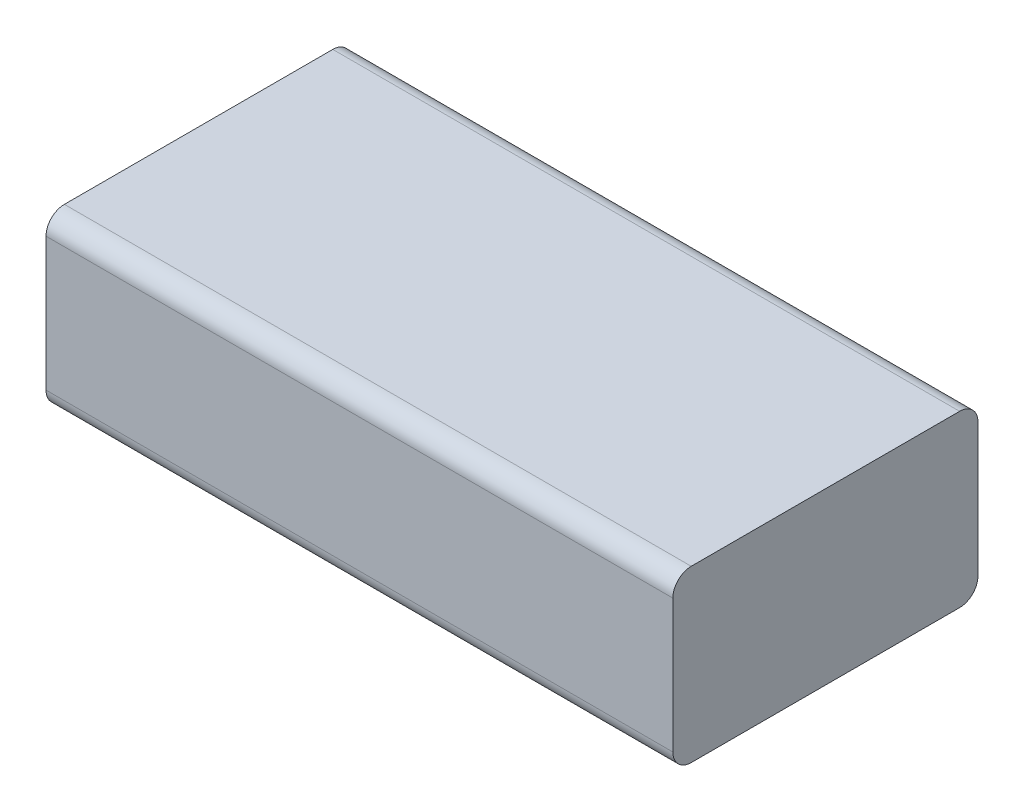
SolidWorks part; units mm, degrees
ref_plane "Front Plane" through (0, 0, 0) normal (0, 0, 1) x (1, 0, 0)
ref_plane "Top Plane" through (0, 0, 0) normal (0, 1, 0) x (1, 0, 0)
ref_plane "Right Plane" through (0, 0, 0) normal (1, 0, 0) x (0, 0, -1)
sketch "Sketch1" plane through (0, 0, 0) normal (0, 1, 0) x (1, 0, 0)
  line L1 (-34.1, -16.6) -> (34.1, -16.6)
  line L2 (-34.1, -16.6) -> (-34.1, 16.6)
  line L3 (-34.1, 16.6) -> (34.1, 16.6)
  line L4 (34.1, -16.6) -> (34.1, 16.6)
  line L5 (-34.1, -16.6) -> (34.1, 16.6) construction
  line L6 (-34.1, 16.6) -> (34.1, -16.6) construction
  point P0 (0, 0)
  dimension "D1" = 68.2
  dimension "D2" = 33.2
extrude "Boss-Extrude1" add sketch "Sketch1" along normal blind 18.5
fillet "Fillet1" radius 2 4 edges at (0, 18.5, -16.6) (0, 0, -16.6) (0, 0, 16.6) (0, 18.5, 16.6)
